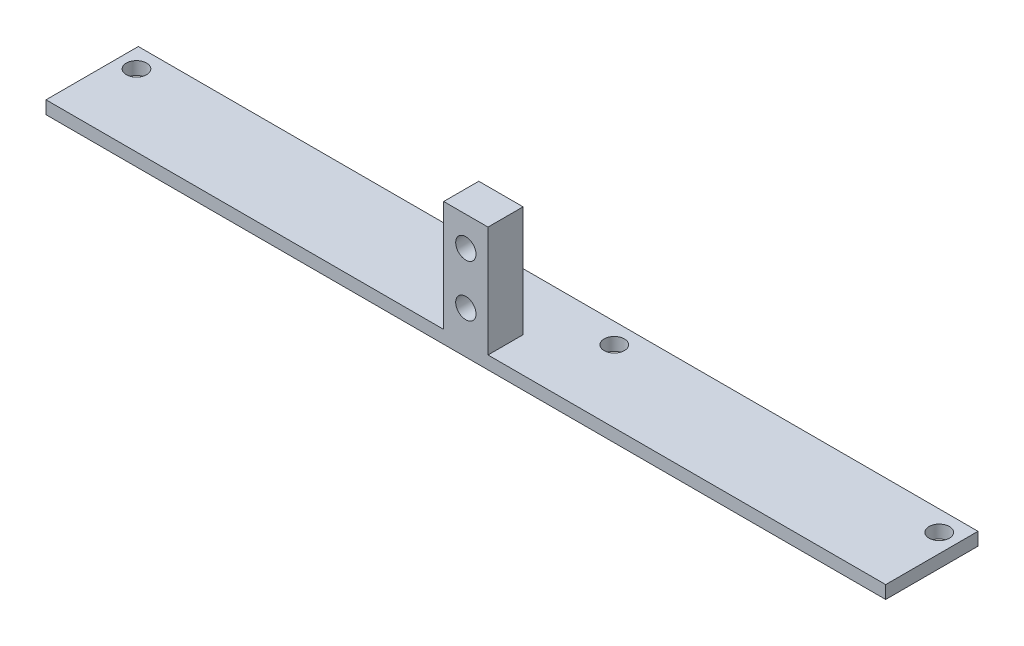
SolidWorks part; units mm, degrees
ref_plane "Front" through (0, 0, 0) normal (0, 0, 1) x (1, 0, 0)
ref_plane "Top" through (0, 0, 0) normal (0, 1, 0) x (1, 0, 0)
ref_plane "Right" through (0, 0, 0) normal (1, 0, 0) x (0, 0, -1)
sketch "Sketch2" plane through (0, 0, 0) normal (0, 1, 0) x (1, 0, 0)
  line L1 (0, 0) -> (114.7, 0)
  line L2 (0, 0) -> (0, 12.5)
  line L3 (0, 12.5) -> (114.7, 12.5)
  line L4 (114.7, 0) -> (114.7, 12.5)
  dimension "D1" = 114.7
  dimension "D2" = 12.5
extrude "bracketBase" add sketch "Sketch2" along normal blind 1.75
sketch "Sketch3" plane through (0, 1.75, 0) normal (0, 1, 0) x (1, 0, 0)
  line L0 (57.35, 12.5) -> (57.35, 0) construction
  line L1 (114.7, 12.5) -> (0, 12.5) construction
  line L2 (0, 0) -> (114.7, 0) construction
  line L3 (0, 12.5) -> (0, 0) construction
  circle A0 centre (3, 9.75) radius 1.375
  circle A1 centre (47, 9.75) radius 1.375
  circle A2 centre (67.7, 9.75) radius 1.375
  circle A3 centre (111.7, 9.75) radius 1.375
  dimension "D1" = 2.75
  dimension "D2" = 2.75
  dimension "D3" = 3
  dimension "D4" = 44
extrude "bottomChassisMountingHoles" cut sketch "Sketch3" against normal blind 1.75
sketch "Sketch4" plane through (0, 0, 0) normal (0, 0, 1) x (1, 0, 0)
  line L0 (57.35, 0) -> (57.35, 26.8195) construction
  line L1 (114.7, 0) -> (120.7, 0)
  line L2 (114.7, 0) -> (114.7, 16.75)
  line L3 (114.7, 16.75) -> (120.7, 16.75)
  line L4 (120.7, 0) -> (120.7, 16.75)
  line L5 (0, 0) -> (114.7, 0) construction
  line L6 (0, 16.75) -> (-6, 16.75)
  line L7 (-6, 0) -> (-6, 16.75)
  line L8 (0, 0) -> (-6, 0)
  line L9 (0, 0) -> (0, 16.75)
  line L11 (54.35, 0) -> (60.35, 0)
  line L12 (54.35, 0) -> (54.35, 16.75)
  line L13 (54.35, 16.75) -> (60.35, 16.75)
  line L14 (60.35, 0) -> (60.35, 16.75)
  point P17 (57.35, 0)
  dimension "D1" = 16.75
  dimension "D2" = 6
extrude "mountingTabs" add sketch "Sketch4" against normal blind 4.75
sketch "Sketch5" plane through (0, 0, -12.5) normal (0, 0, -1) x (-1, 0, 0)
  line L0 (-120.7, 0) -> (-120.7, 16.75) construction
  line L1 (-114.7, 0) -> (-120.7, 0)
  line L2 (-114.7, 0) -> (-114.7, 1.75)
  line L3 (-114.7, 1.75) -> (-120.7, 1.75)
  line L4 (-120.7, 0) -> (-120.7, 1.75)
  line L5 (-114.7, 1.75) -> (0, 1.75) construction
  line L6 (6, 16.75) -> (6, 0) construction
  line L7 (0, 0) -> (6, 0)
  line L8 (0, 0) -> (0, 1.75)
  line L9 (0, 1.75) -> (6, 1.75)
  line L10 (6, 0) -> (6, 1.75)
extrude "extension" add sketch "Sketch5" against normal up to surface (7.75 mm away) up to face at (-2.4, 7.05, -4.75)
sketch "Sketch6" plane through (0, 0, -4.75) normal (0, 0, -1) x (-1, 0, 0)
  line L0 (-57.35, 0) -> (-57.35, 1.75) construction
  line L1 (-120.7, 0) -> (6, 0) construction
  line L2 (-54.35, 1.75) -> (-60.35, 1.75) construction
  line L3 (-60.35, 16.75) -> (-54.35, 16.75) construction
  line L4 (-120.7, 16.75) -> (-114.7, 16.75) construction
  circle A0 centre (-57.35, 12.75) radius 1.375
  circle A1 centre (-57.35, 5.75) radius 1.375
  circle A2 centre (-117.7, 12.75) radius 1.375
  circle A3 centre (-117.7, 5.75) radius 1.375
  circle A4 centre (3, 5.75) radius 1.375
  circle A5 centre (3, 12.75) radius 1.375
  point P12 (-57.35, 16.75)
  point P19 (-117.7, 16.75)
  dimension "D1" = 2.75
  dimension "D2" = 4
  dimension "D3" = 7
extrude "rearShellMountingHoles" cut sketch "Sketch6" against normal blind 4.75
sketch "Sketch8" plane through (0, 1.75, 0) normal (0, 1, 0) x (1, 0, 0)
  line L0 (57.35, 12.5) -> (57.35, 5.75) construction
  line L1 (120.7, 12.5) -> (-6, 12.5) construction
  line L2 (53.35, 5.75) -> (61.35, 5.75) construction
  line L3 (120.7, 4.75) -> (120.7, 12.5) construction
  circle A0 centre (120.95, 8.5675) radius 3.25
  circle A1 centre (-6.25, 8.5675) radius 3.25
  dimension "D1" = 6.5
  dimension "D2" = 3.9325
  dimension "D3" = 0.25
extrude "Cut-Extrude2" cut sketch "Sketch8" against normal blind 10
sketch "Sketch9" plane through (0, 1.75, 0) normal (0, -1, 0) x (1, 0, 0)
  line L0 (120.7, -5.3271) -> (122.423, -5.1942)
  line L1 (122.423, -5.1942) -> (122.9332, -11.8079)
  line L2 (122.9332, -11.8079) -> (120.7, -11.8079)
  arc A0 (120.7, -5.3271) -> (120.7, -11.8079) centre (120.95, -8.5675) ccw construction
  arc A1 (120.7, -5.3271) -> (120.7, -11.8079) centre (120.95, -8.5675) ccw
  circle A2 centre (-6.25, -8.5675) radius 3.25
  arc A3 (-6, -11.8079) -> (-6, -5.3271) centre (-6.25, -8.5675) ccw construction
extrude "Cut-Extrude3" cut sketch "Sketch9" against normal blind 10
sketch "Sketch10" plane through (0, 1.75, 0) normal (0, 1, 0) x (1, 0, 0)
  line L0 (57.35, 12.5) -> (57.35, 0) construction
  line L1 (120.7, 12.5) -> (114.2, 12.5)
  line L2 (120.7, 12.5) -> (120.7, 0)
  line L3 (120.7, 0) -> (114.2, 0)
  line L4 (114.2, 12.5) -> (114.2, 0)
  line L5 (120.7, 12.5) -> (-6, 12.5) construction
  line L6 (60.35, 0) -> (54.35, 0) construction
  line L7 (61.35, 0) -> (113.7, 0) construction
  line L8 (-6, 0) -> (0.5, 0)
  line L9 (0.5, 12.5) -> (0.5, 0)
  line L10 (-6, 12.5) -> (0.5, 12.5)
  line L11 (-6, 12.5) -> (-6, 0)
  dimension "D1" = 6.5
extrude "Cut-Extrude4" cut sketch "Sketch10" against normal through all both and the other way through all
